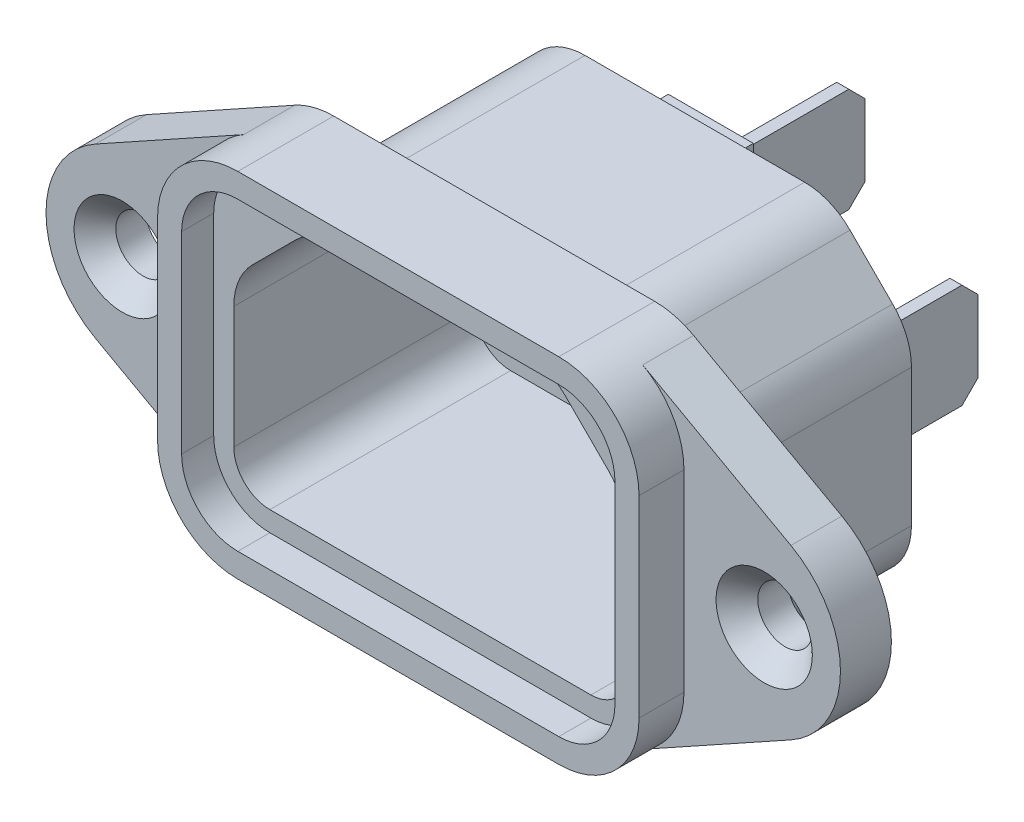
SolidWorks part; units mm, degrees
ref_plane "Front Plane" through (0, 0, 0) normal (0, 0, 1) x (1, 0, 0)
ref_plane "Top Plane" through (0, 0, 0) normal (0, 1, 0) x (1, 0, 0)
ref_plane "Right Plane" through (0, 0, 0) normal (1, 0, 0) x (0, 0, -1)
sketch "Sketch1" plane through (0, 0, 0) normal (0, 0, 1) x (1, 0, 0)
  line L1 (24.75, -11) -> (-24.75, -11)
  line L2 (24.75, -11) -> (24.75, 11)
  line L3 (24.75, 11) -> (-24.75, 11)
  line L4 (-24.75, -11) -> (-24.75, 11)
  line L5 (24.75, -11) -> (-24.75, 11) construction
  line L6 (24.75, 11) -> (-24.75, -11) construction
  point P0 (0, 0)
  dimension "D1" = 49.5
  dimension "D2" = 22
extrude "Boss-Extrude1" add sketch "Sketch1" along normal blind 3.175
sketch "Sketch2" plane through (0, 0, 3.175) normal (0, 0, 1) x (1, 0, 0)
  line L0 (24.75, 11) -> (-24.75, 11) construction
  line L1 (15, -11) -> (-15, -11)
  line L2 (15, -11) -> (15, 11)
  line L3 (15, 11) -> (-15, 11)
  line L4 (-15, -11) -> (-15, 11)
  line L5 (15, -11) -> (-15, 11) construction
  line L6 (15, 11) -> (-15, -11) construction
  point P0 (0, 0)
  dimension "D1" = 30
extrude "Boss-Extrude2" add sketch "Sketch2" along normal blind 2.8
fillet "Fillet1" radius 5 4 edges
sketch "Sketch4" plane through (0, 0, 0) normal (0, 0, -1) x (-1, 0, 0)
  line L1 (13.5, -9.6) -> (-13.5, -9.6)
  line L2 (13.5, -9.6) -> (13.5, 9.6)
  line L3 (13.5, 9.6) -> (-13.5, 9.6)
  line L4 (-13.5, -9.6) -> (-13.5, 9.6)
  line L5 (13.5, -9.6) -> (-13.5, 9.6) construction
  line L6 (13.5, 9.6) -> (-13.5, -9.6) construction
  point P0 (0, 0)
  dimension "D1" = 27
  dimension "D2" = 19.2
extrude "Boss-Extrude3" add sketch "Sketch4" along normal blind 12.5
chamfer "Chamfer1" distance 5 angle 45 2 edges at (-13.5, 9.6, -6.25) (13.5, 9.6, -6.25)
fillet "Fillet2" radius 4 6 edges at (13.5, -9.6, -6.25) (-13.5, -9.6, -6.25) (-13.5, 4.6, -6.25) (-8.5, 9.6, -6.25) (8.5, 9.6, -6.25) (13.5, 4.6, -6.25)
sketch "Sketch3" plane through (0, 0, 3.175) normal (0, 0, 1) x (1, 0, 0)
  line L0 (20, 0) -> (-20, 0) construction
  circle A0 centre (-20, 0) radius 1.7
  circle A1 centre (20, 0) radius 1.7
  point P8 (0, 0)
  dimension "D2" = 3.4
  dimension "D1" = 40
extrude "Cut-Extrude1" cut sketch "Sketch3" against normal through all
sketch "Sketch5" plane through (0, 0, 3.175) normal (0, 0, 1) x (1, 0, 0)
  line L0 (-24.75, 11) -> (-24.75, -11) construction
  line L3 (-12.4264, 10.3718) -> (-21.6617, 5.2462)
  line L4 (-10, 11) -> (-24.75, 11)
  line L5 (-24.75, 11) -> (-24.75, 0)
  arc A0 (-21.6617, 5.2462) -> (-24.75, 0) centre (-18.75, 0) ccw
  arc A1 (-10, 11) -> (-15, 6) centre (-10, 6) ccw construction
  arc A2 (-10, 11) -> (-12.4264, 10.3718) centre (-10, 6) ccw
  dimension "D1" = 12
extrude "Cut-Extrude2" cut sketch "Sketch5" against normal blind 16.2
mirror "Mirror1" about plane through (0, 0, 0) normal (0, 1, 0) of "Cut-Extrude2"
mirror "Mirror2" about plane through (0, 0, 0) normal (1, 0, 0) of "Mirror1", "Cut-Extrude2"
chamfer "Chamfer2" distance 1.3 angle 45 2 edges at (21.7, 0, 3.175) (-18.3, 0, 3.175)
sketch "Sketch8" plane through (0, 0, 5.975) normal (0, 0, 1) x (1, 0, 0)
  line L0 (-7.25, 8.25) -> (-12.25, 3.25)
  line L1 (12.25, 3.25) -> (7.25, 8.25)
  line L8 (10, 8.25) -> (-10, 8.25)
  line L9 (-12.25, 6) -> (-12.25, -6)
  line L10 (-10, -8.25) -> (10, -8.25)
  line L11 (12.25, -6) -> (12.25, 6)
  line L12 (7.25, 8.25) -> (-7.25, 8.25)
  line L13 (-12.25, 3.25) -> (-12.25, -6)
  line L14 (-10, -8.25) -> (10, -8.25)
  line L15 (12.25, -6) -> (12.25, 3.25)
  arc A8 (-10, 8.25) -> (-12.25, 6) centre (-10, 6) ccw
  arc A9 (-12.25, -6) -> (-10, -8.25) centre (-10, -6) ccw
  arc A10 (10, -8.25) -> (12.25, -6) centre (10, -6) ccw
  arc A11 (12.25, 6) -> (10, 8.25) centre (10, 6) ccw
  arc A13 (-12.25, -6) -> (-10, -8.25) centre (-10, -6) ccw
  arc A14 (10, -8.25) -> (12.25, -6) centre (10, -6) ccw
  point P4 (-12.25, 8.25)
  point P7 (12.25, 8.25)
  dimension "D1" = 2.75
extrude "Cut-Extrude4" cut sketch "Sketch8" against normal blind 17
fillet "Fillet3" radius 4 4 edges at (-12.25, 3.25, -2.525) (12.25, 3.25, -2.525) (7.25, 8.25, -2.525) (-7.25, 8.25, -2.525)
sketch "Sketch9" plane through (0, 0, -12.5) normal (0, 0, -1) x (-1, 0, 0)
  line L0 (6.8431, 9.6) -> (-6.8431, 9.6) construction
  line L1 (2.65, -2.05) -> (-2.65, -2.05)
  line L2 (2.65, -2.05) -> (2.65, 9.1)
  line L3 (2.65, 9.1) -> (-2.65, 9.1)
  line L4 (-2.65, -2.05) -> (-2.65, 9.1)
  line L5 (2.65, -2.05) -> (-2.65, 9.1) construction
  line L6 (2.65, 9.1) -> (-2.65, -2.05) construction
  line L7 (-9.5, -9.6) -> (9.5, -9.6) construction
  line L8 (-4.4, -9.1) -> (-9.7, -9.1)
  line L9 (-4.4, -9.1) -> (-4.4, 2.05)
  line L10 (-4.4, 2.05) -> (-9.7, 2.05)
  line L11 (-9.7, -9.1) -> (-9.7, 2.05)
  line L12 (-4.4, -9.1) -> (-9.7, 2.05) construction
  line L13 (-4.4, 2.05) -> (-9.7, -9.1) construction
  line L14 (9.7, -9.1) -> (4.4, -9.1)
  line L15 (9.7, -9.1) -> (9.7, 2.05)
  line L16 (9.7, 2.05) -> (4.4, 2.05)
  line L17 (4.4, -9.1) -> (4.4, 2.05)
  line L18 (9.7, -9.1) -> (4.4, 2.05) construction
  line L19 (9.7, 2.05) -> (4.4, -9.1) construction
  point P0 (0, 3.525)
  point P5 (0, 9.6)
  point P8 (-7.05, -3.525)
  point P14 (7.05, -3.525)
  dimension "D1" = 0.5
  dimension "D2" = 5.3
  dimension "D3" = 11.15
  dimension "D4" = 1.75
  dimension "D5" = 1.75
  dimension "D6" = 0.5
extrude "Boss-Extrude4" add sketch "Sketch9" along normal blind 1
sketch "Sketch10" plane through (0, 0, -13.5) normal (0, 0, -1) x (-1, 0, 0)
  line L0 (0, 3.525) -> (-2.65, 3.525) construction
  line L1 (0.375, 0.275) -> (-0.375, 0.275)
  line L2 (0.375, 0.275) -> (0.375, 6.775)
  line L3 (0.375, 6.775) -> (-0.375, 6.775)
  line L4 (-0.375, 0.275) -> (-0.375, 6.775)
  line L5 (0.375, 0.275) -> (-0.375, 6.775) construction
  line L6 (0.375, 6.775) -> (-0.375, 0.275) construction
  line L7 (-6.675, -6.775) -> (-7.425, -6.775)
  line L8 (-6.675, -6.775) -> (-6.675, -0.275)
  line L9 (-6.675, -0.275) -> (-7.425, -0.275)
  line L10 (-7.425, -6.775) -> (-7.425, -0.275)
  line L11 (-6.675, -6.775) -> (-7.425, -0.275) construction
  line L12 (-6.675, -0.275) -> (-7.425, -6.775) construction
  line L13 (7.425, -6.775) -> (6.675, -6.775)
  line L14 (7.425, -6.775) -> (7.425, -0.275)
  line L15 (7.425, -0.275) -> (6.675, -0.275)
  line L16 (6.675, -6.775) -> (6.675, -0.275)
  line L17 (7.425, -6.775) -> (6.675, -0.275) construction
  line L18 (7.425, -0.275) -> (6.675, -6.775) construction
  line L19 (-2.65, 9.1) -> (-2.65, -2.05) construction
  line L20 (0, 6.775) -> (0, 9.1) construction
  line L21 (2.65, 9.1) -> (-2.65, 9.1) construction
  line L22 (-7.05, -0.275) -> (-7.05, 2.05) construction
  line L23 (-4.4, 2.05) -> (-9.7, 2.05) construction
  line L24 (-7.425, -3.525) -> (-9.7, -3.525) construction
  line L25 (-9.7, 2.05) -> (-9.7, -9.1) construction
  line L26 (7.05, -0.275) -> (7.05, 2.05) construction
  line L27 (9.7, 2.05) -> (4.4, 2.05) construction
  point P0 (0, 3.525)
  point P5 (-7.05, -3.525)
  point P10 (7.05, -3.525)
  dimension "D1" = 6.5
  dimension "D2" = 0.75
extrude "Boss-Extrude5" add sketch "Sketch10" along normal blind 9.22
chamfer "Chamfer3" distance 1 angle 45 6 edges at (7.05, -0.275, -22.72) (7.05, -6.775, -22.72) (0, 0.275, -22.72) (0, 6.775, -22.72) (-7.05, -0.275, -22.72) (-7.05, -6.775, -22.72)
sketch "Sketch6" plane through (0, 0, 5.975) normal (0, 0, 1) x (1, 0, 0)
  line L0 (-13.5, 6) -> (-13.5, -6)
  line L1 (-10, -9.5) -> (10, -9.5)
  line L2 (13.5, -6) -> (13.5, 6)
  line L3 (10, 9.5) -> (-10, 9.5)
  line L4 (10, 11) -> (-10, 11)
  line L5 (-15, 6) -> (-15, -6)
  line L6 (-10, -11) -> (10, -11)
  line L7 (15, -6) -> (15, 6)
  line L8 (10, 11) -> (-10, 11) construction
  line L9 (-15, 6) -> (-15, -6) construction
  line L10 (-10, -11) -> (10, -11) construction
  line L11 (15, -6) -> (15, 6) construction
  arc A0 (-10, 9.5) -> (-13.5, 6) centre (-10, 6) ccw
  arc A1 (-13.5, -6) -> (-10, -9.5) centre (-10, -6) ccw
  arc A2 (10, -9.5) -> (13.5, -6) centre (10, -6) ccw
  arc A3 (13.5, 6) -> (10, 9.5) centre (10, 6) ccw
  arc A4 (-10, 11) -> (-15, 6) centre (-10, 6) ccw
  arc A5 (-15, -6) -> (-10, -11) centre (-10, -6) ccw
  arc A6 (10, -11) -> (15, -6) centre (10, -6) ccw
  arc A7 (15, 6) -> (10, 11) centre (10, 6) ccw
  arc A8 (-10, 11) -> (-15, 6) centre (-10, 6) ccw construction
  arc A9 (-15, -6) -> (-10, -11) centre (-10, -6) ccw construction
  arc A10 (10, -11) -> (15, -6) centre (10, -6) ccw construction
  arc A11 (15, 6) -> (10, 11) centre (10, 6) ccw construction
  dimension "D1" = 0
  dimension "D2" = 1.5
extrude "Cut-Extrude3" cut sketch "Sketch6" against normal blind 2
